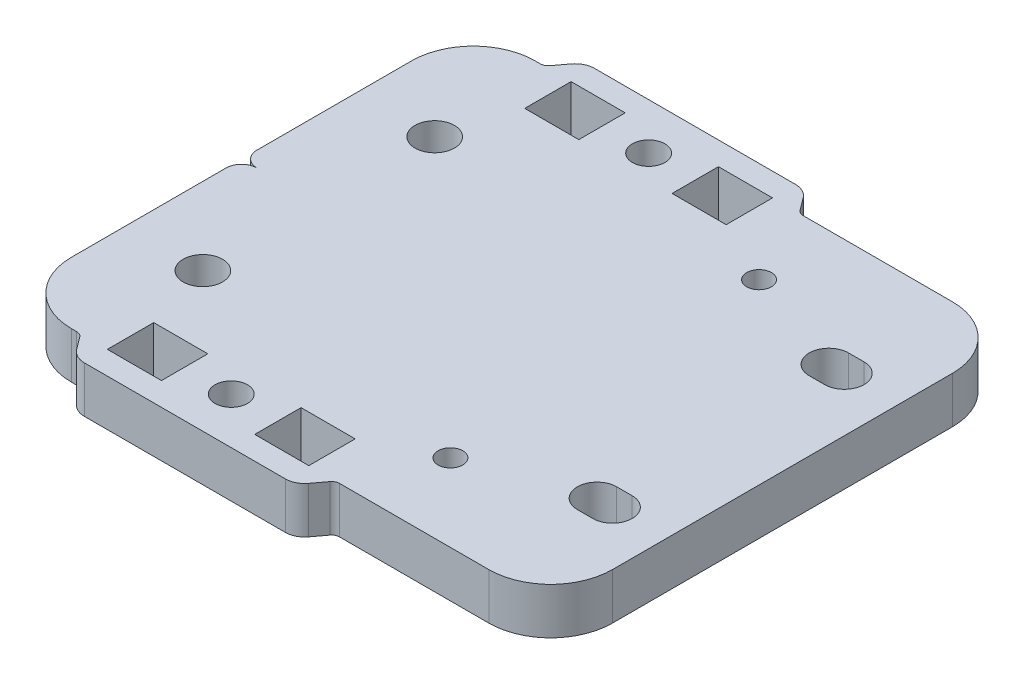
SolidWorks part; units mm, degrees
material "Клен"
ref_plane "Спереди" through (0, 0, 0) normal (0, 0, 1) x (1, 0, 0)
ref_plane "Сверху" through (0, 0, 0) normal (0, 1, 0) x (1, 0, 0)
ref_plane "Справа" through (0, 0, 0) normal (1, 0, 0) x (0, 0, -1)
sketch "Эскиз1" plane through (0, 0, 0) normal (0, 1, 0) x (1, 0, 0)
  line L0 (-41.181, -0.0464) -> (44.1026, -0.0464) construction
  line L10 (-27, -30) -> (27, -30)
  line L11 (-35, -22) -> (-35, 22)
  line L12 (-27, 30) -> (27, 30)
  line L13 (35, -22) -> (35, 22)
  line L14 (-35, -30) -> (35, 30) construction
  line L15 (-35, 30) -> (35, -30) construction
  arc A4 (27, 30) -> (35, 22) centre (27, 22) cw
  arc A5 (27, -30) -> (35, -22) centre (27, -22) ccw
  arc A6 (-27, -30) -> (-35, -22) centre (-27, -22) cw
  arc A7 (-35, 22) -> (-27, 30) centre (-27, 22) cw
  point P0 (0, 0)
  dimension "D1" = 8
  dimension "D2" = 60
  dimension "D3" = 70
extrude "Бобышка-Вытянуть1" add sketch "Эскиз1" along normal blind 6
sketch "Эскиз2" plane through (0, 0, 0) normal (0, -1, 0) x (1, 0, 0)
  line L0 (0, -37.0349) -> (0, 29.2907) construction
  line L1 (28, -15) -> (26, -15) construction
  line L2 (28, -17.55) -> (26, -17.55)
  line L3 (28, -12.45) -> (26, -12.45)
  line L6 (-46.1924, 0) -> (55.6646, 0) construction
  line L7 (28, 15) -> (26, 15) construction
  line L8 (28, 17.55) -> (26, 17.55)
  line L9 (28, 12.45) -> (26, 12.45)
  line L10 (-35, -22) -> (-35, 22) construction
  circle A0 centre (-25, -15) radius 2.55
  arc A1 (28, -17.55) -> (28, -12.45) centre (28, -15) ccw
  arc A2 (26, -12.45) -> (26, -17.55) centre (26, -15) ccw
  arc A3 (28, 17.55) -> (28, 12.45) centre (28, 15) cw
  arc A4 (26, 12.45) -> (26, 17.55) centre (26, 15) cw
  circle A5 centre (-25, 15) radius 2.55
  circle A6 centre (12, 19.9667) radius 1.6
  circle A7 centre (12, -19.9667) radius 1.6
  point P7 (27, -15)
  point P12 (27, -17.55)
  point P13 (12, 19.9667)
  point P21 (27, 15)
  dimension "D1" = 5.1
  dimension "D2" = 5.1
  dimension "D3" = 2
  dimension "D4" = 53
  dimension "D5" = 10
  dimension "D6" = 30
extrude "Вырез-Вытянуть1" cut sketch "Эскиз2" against normal through all
sketch "Эскиз3" plane through (0, 0, 0) normal (0, -1, 0) x (1, 0, 0)
  line L0 (-33, 0) -> (27.7687, 0) construction
  line L1 (-35, -22) -> (-35, 22) construction
  line L2 (-35, -2) -> (-35, 2)
  arc A0 (-33, 0) -> (-35, -2) centre (-33, -2) ccw
  arc A1 (-33, 0) -> (-35, 2) centre (-33, 2) cw
  point P3 (-35, -2)
  point P4 (-33, 0)
  point P7 (-35, 2)
  dimension "D2" = 2
  dimension "D1" = 2
extrude "Вырез-Вытянуть2" cut sketch "Эскиз3" against normal through all
sketch "Эскиз21" plane through (-9.3228, 6, 20) normal (0, -1, 0) x (-1, 0, 0)
  line L0 (-13, 53) -> (13, 53)
  line L1 (0, -102.8936) -> (0, 112.5572) construction
  line L2 (15, 52) -> (16.2, 50.4)
  line L4 (17, 50) -> (-17, 50)
  line L5 (-15, 52) -> (-16.2, 50.4)
  arc A6 (13, 53) -> (15, 52) centre (13, 50.5) cw
  arc A7 (16.2, 50.4) -> (17, 50) centre (17, 51) ccw
  arc A8 (-13, 53) -> (-15, 52) centre (-13, 50.5) ccw
  arc A9 (-16.2, 50.4) -> (-17, 50) centre (-17, 51) cw
  point P12 (0, 53)
  point P13 (14.118, 52.7361)
  point P15 (-14.118, 52.7361)
  point P17 (0, 50)
  point P21 (14.118, 52.7361)
  dimension "D1" = 17
  dimension "D4" = 2.5
  dimension "D5" = 1
  dimension "D2" = 13
extrude "Бобышка-Вытянуть2" add sketch "Эскиз21" along normal blind 6
sketch "Эскиз31" plane through (-9.3228, 0, 20) normal (0, -1, 0) x (-1, 0, 0)
  line L0 (0, -127.8936) -> (0, 87.5572) construction
  line L1 (13.0318, 50) -> (6.0318, 50)
  line L2 (13.0318, 50) -> (13.0318, 44)
  line L3 (13.0318, 44) -> (6.0318, 44)
  line L4 (6.0318, 50) -> (6.0318, 44)
  line L5 (-13.0318, 44) -> (-6.0318, 44)
  line L6 (-13.0318, 50) -> (-13.0318, 44)
  line L7 (-6.0318, 50) -> (-6.0318, 44)
  line L8 (-13.0318, 50) -> (-6.0318, 50)
  circle A0 centre (0, 47) radius 2.1
  dimension "D1" = 4.2
extrude "Вырез-Вытянуть11" cut sketch "Эскиз31" against normal through all
other "Авто-элемент1<DIN 7991-3>"
sketch "Эскиз22" plane through (-9.3228, 6, -20) normal (0, -1, 0) x (1, 0, 0)
  line L0 (-13, 53) -> (13, 53)
  line L1 (0, -102.8936) -> (0, 112.5572) construction
  line L2 (15, 52) -> (16.2, 50.4)
  line L4 (17, 50) -> (-17, 50)
  line L5 (-15, 52) -> (-16.2, 50.4)
  arc A6 (13, 53) -> (15, 52) centre (13, 50.5) cw
  arc A7 (16.2, 50.4) -> (17, 50) centre (17, 51) ccw
  arc A8 (-13, 53) -> (-15, 52) centre (-13, 50.5) ccw
  arc A9 (-16.2, 50.4) -> (-17, 50) centre (-17, 51) cw
  point P12 (0, 53)
  point P13 (14.118, 52.7361)
  point P15 (-14.118, 52.7361)
  point P17 (0, 50)
  point P21 (14.118, 52.7361)
  dimension "D1" = 17
  dimension "D4" = 2.5
  dimension "D5" = 1
  dimension "D2" = 13
extrude "Бобышка-Вытянуть21" add sketch "Эскиз22" along normal blind 6
sketch "Эскиз33" plane through (-9.3228, 0, -20) normal (0, -1, 0) x (1, 0, 0)
  line L0 (0, -127.8936) -> (0, 87.5572) construction
  line L1 (13.0318, 50) -> (6.0318, 50)
  line L2 (13.0318, 50) -> (13.0318, 44)
  line L3 (13.0318, 44) -> (6.0318, 44)
  line L4 (6.0318, 50) -> (6.0318, 44)
  line L5 (-13.0318, 44) -> (-6.0318, 44)
  line L6 (-13.0318, 50) -> (-13.0318, 44)
  line L7 (-6.0318, 50) -> (-6.0318, 44)
  line L8 (-13.0318, 50) -> (-6.0318, 50)
  circle A0 centre (0, 47) radius 2.1
  dimension "D1" = 4.2
extrude "Вырез-Вытянуть13" cut sketch "Эскиз33" against normal through all
other "Авто-элемент1<DIN 7991-4>"
equation "\"D2@Эскиз2\"=\"D1@Эскиз2\""
